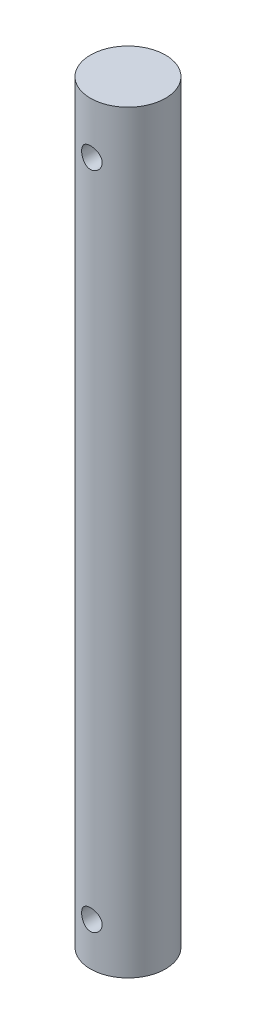
SolidWorks part; units mm, degrees
ref_plane "Front" through (0, 0, 0) normal (0, 0, 1) x (1, 0, 0)
ref_plane "Top" through (0, 0, 0) normal (0, 1, 0) x (1, 0, 0)
ref_plane "Right" through (0, 0, 0) normal (1, 0, 0) x (0, 0, -1)
sketch "Sketch1" plane through (0, 0, 0) normal (0, 1, 0) x (1, 0, 0)
  circle A0 centre (0, 0) radius 5.5562
  dimension "D1" = 11.1125
extrude "Boss-Extrude1" add sketch "Sketch1" along normal blind 111.76
ref_plane "Plane1" through (0, 0, 5.5562) normal (0, 0, 1) x (1, 0, 0)
hole_wizard "#31 (0.12) Diameter Hole1" positions "Sketch2" profile "Sketch3" hole size "#31" standard "ANSI Inch" end condition through all
sketch "Sketch2" plane through (0, 0, 5.5562) normal (0, 0, 1) x (1, 0, 0)
  line L0 (5.5562, 111.76) -> (-5.5562, 111.76) construction
  line L1 (5.5562, 111.76) -> (-5.5562, 111.76)
  line L2 (0, 104.14) -> (0, 111.76)
  line L4 (-5.5562, 0) -> (5.5562, 0) construction
  line L5 (-5.5562, 0) -> (5.5562, 0)
  line L7 (0, 6.35) -> (0, 0)
  point P0 (0, 104.14)
  point P2 (0, 6.35)
  dimension "D1" = 7.62
  dimension "D2" = 6.35
sketch "Sketch3" plane through (0, 104.14, 5.5562) normal (1, 0, 0) x (0, -1, 0)
  line L0 (0, 0) -> (0, 11.1125)
  line L1 (0, 11.1125) -> (1.524, 11.1125)
  line L2 (1.524, 11.1125) -> (1.524, 0)
  line L5 (1.524, 0) -> (0, 0)
  line L11 (0, -6.35) -> (0, 107.95) construction
  dimension "Thru Hole Dia." = 3.048
  dimension "Thru Hole Depth" = 11.1125
